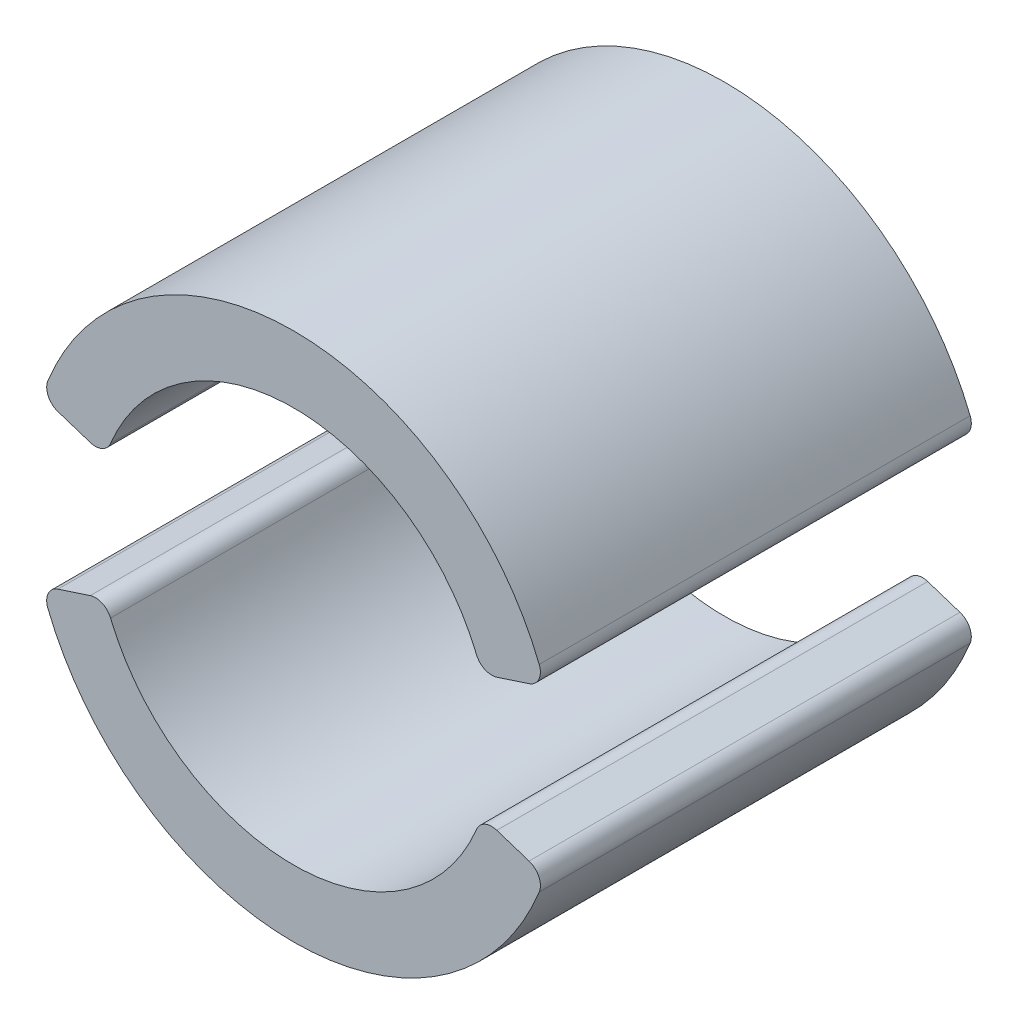
SolidWorks part; units mm, degrees
ref_plane "Front Plane" through (0, 0, 0) normal (0, 0, 1) x (1, 0, 0)
ref_plane "Top Plane" through (0, 0, 0) normal (0, 1, 0) x (1, 0, 0)
ref_plane "Right Plane" through (0, 0, 0) normal (1, 0, 0) x (0, 0, -1)
sketch "Sketch1" plane through (0, 0, 0) normal (0, 0, 1) x (1, 0, 0)
  line L0 (0, 0) -> (-28.3604, 0) construction
  line L1 (0, 0) -> (0, -23.8559) construction
  line L2 (-12.5803, 4.1031) -> (-14.5776, 4.7545)
  line L3 (12.5803, 4.1031) -> (14.5776, 4.7545)
  line L4 (12.5803, -4.1031) -> (14.5776, -4.7545)
  line L5 (-12.5803, -4.1031) -> (-14.5776, -4.7545)
  arc A0 (-15.2056, -6.0987) -> (15.2056, -6.0987) centre (0, 0) ccw
  arc A1 (-11.3263, -4.681) -> (11.3263, -4.681) centre (0, 0) ccw
  arc A2 (11.3263, 4.681) -> (-11.3263, 4.681) centre (0, 0) ccw
  arc A3 (15.2056, 6.0987) -> (-15.2056, 6.0987) centre (0, 0) ccw
  arc A4 (-11.3263, -4.681) -> (-12.5803, -4.1031) centre (-12.2653, -5.069) ccw
  arc A5 (-14.5776, -4.7545) -> (-15.2056, -6.0987) centre (-14.2626, -5.7205) ccw
  arc A6 (14.5776, -4.7545) -> (15.2056, -6.0987) centre (14.2626, -5.7205) cw
  arc A7 (12.5803, -4.1031) -> (11.3263, -4.681) centre (12.2653, -5.069) ccw
  arc A8 (14.5776, 4.7545) -> (15.2056, 6.0987) centre (14.2626, 5.7205) ccw
  arc A9 (12.5803, 4.1031) -> (11.3263, 4.681) centre (12.2653, 5.069) cw
  arc A10 (-12.5803, 4.1031) -> (-11.3263, 4.681) centre (-12.2653, 5.069) ccw
  arc A11 (-14.5776, 4.7545) -> (-15.2056, 6.0987) centre (-14.2626, 5.7205) cw
  point P18 (-15.5755, -5.08)
  point P21 (15.5755, -5.08)
  point P26 (15.5755, 5.08)
  point P29 (11.6514, 3.8002)
  point P34 (-15.5755, 5.08)
  dimension "D1" = 32.766
  dimension "D2" = 24.511
  dimension "D4" = 1.016
  dimension "D3" = 5.08
extrude "Boss-Extrude1" add sketch "Sketch1" along normal blind 26.67
